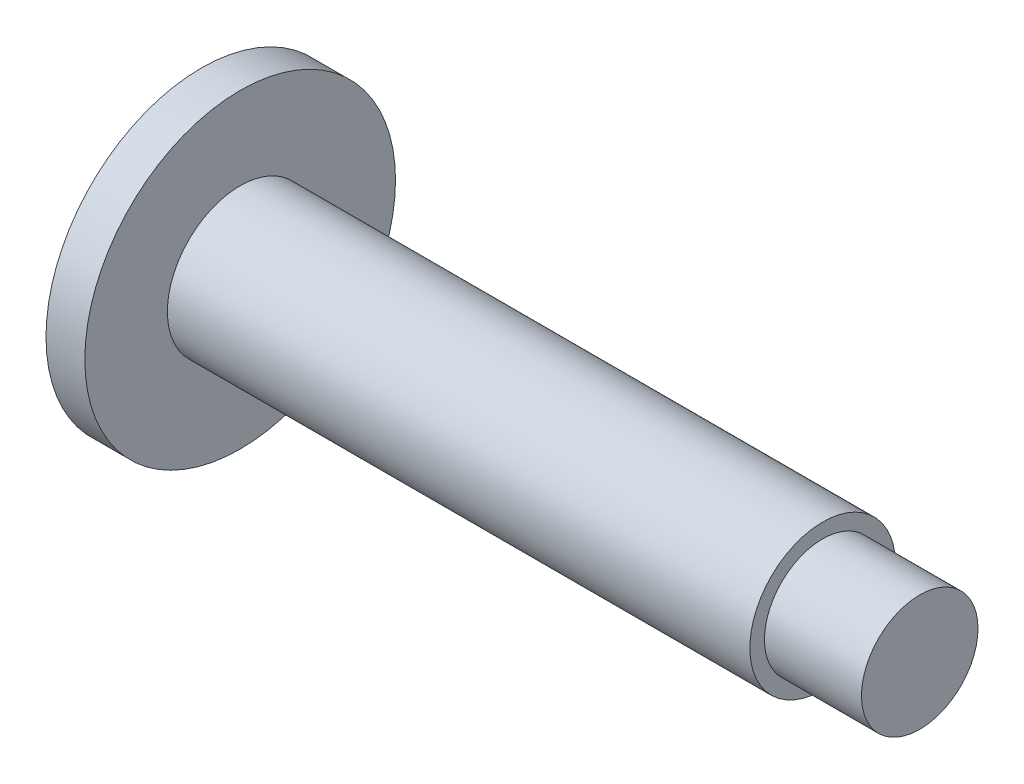
SolidWorks part; units mm, degrees
ref_plane "Alzado" through (0, 0, 0) normal (0, 0, 1) x (1, 0, 0)
ref_plane "Planta" through (0, 0, 0) normal (0, 1, 0) x (1, 0, 0)
ref_plane "Vista lateral" through (0, 0, 0) normal (1, 0, 0) x (0, 0, -1)
sketch "Croquis1" plane through (0, 0, 0) normal (1, 0, 0) x (0, 0, -1)
  circle A0 centre (0, 0) radius 8
  dimension "D1" = 16
extrude "Saliente-Extruir1" add sketch "Croquis1" along normal blind 2
sketch "Croquis2" plane through (2, 0, 0) normal (1, 0, 0) x (0, 0, -1)
  circle A0 centre (0, 0) radius 3.75
  dimension "D1" = 7.5
extrude "Saliente-Extruir2" add sketch "Croquis2" along normal blind 30
sketch "Croquis3" plane through (32, 0, 0) normal (1, 0, 0) x (0, 0, -1)
  circle A0 centre (0, 0) radius 3
  dimension "D1" = 6
extrude "Saliente-Extruir3" add sketch "Croquis3" along normal blind 5
